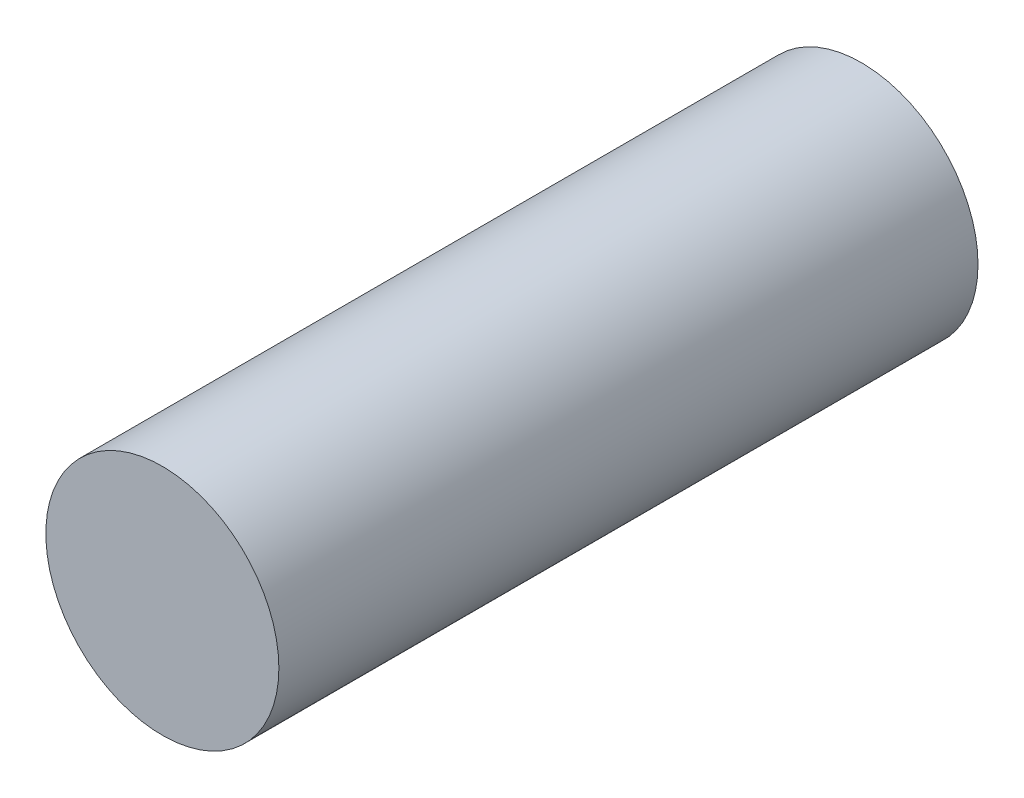
SolidWorks part; units mm, degrees
ref_plane "前基準面" through (0, 0, 0) normal (0, 0, 1) x (1, 0, 0)
ref_plane "上基準面" through (0, 0, 0) normal (0, 1, 0) x (1, 0, 0)
ref_plane "右基準面" through (0, 0, 0) normal (1, 0, 0) x (0, 0, -1)
sketch "草圖1" plane through (0, 0, 0) normal (0, 0, 1) x (1, 0, 0)
  circle A0 centre (0, 0) radius 2.5
  dimension "D1" = 5
extrude "填料-伸長1" add sketch "草圖1" along normal blind 15
